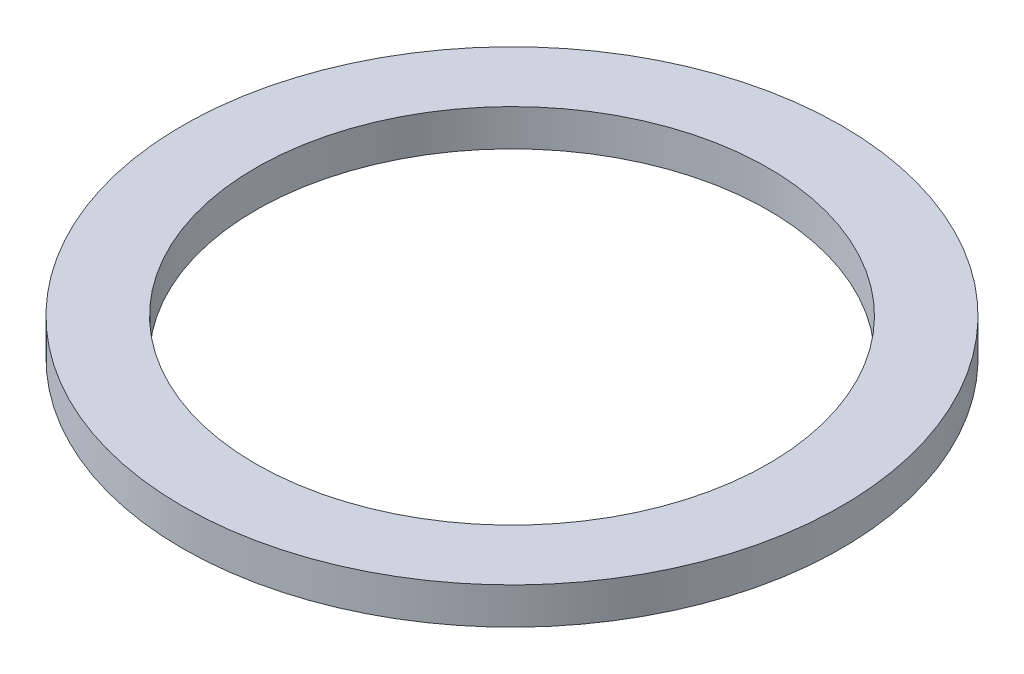
SolidWorks part; units mm, degrees
material "Acrílico (Impacto medio-alto)"
ref_plane "Alzado" through (0, 0, 0) normal (0, 0, 1) x (1, 0, 0)
ref_plane "Planta" through (0, 0, 0) normal (0, 1, 0) x (1, 0, 0)
ref_plane "Vista lateral" through (0, 0, 0) normal (1, 0, 0) x (0, 0, -1)
sketch "Croquis1" plane through (0, 0, 0) normal (0, 1, 0) x (1, 0, 0)
  circle A0 centre (0, 0) radius 45
  circle A1 centre (0, 0) radius 35
  dimension "D1" = 90
  dimension "D2" = 10
extrude "Saliente-Extruir1" add sketch "Croquis1" along normal blind 5 contours A1
equation "\"e\" = 5"
